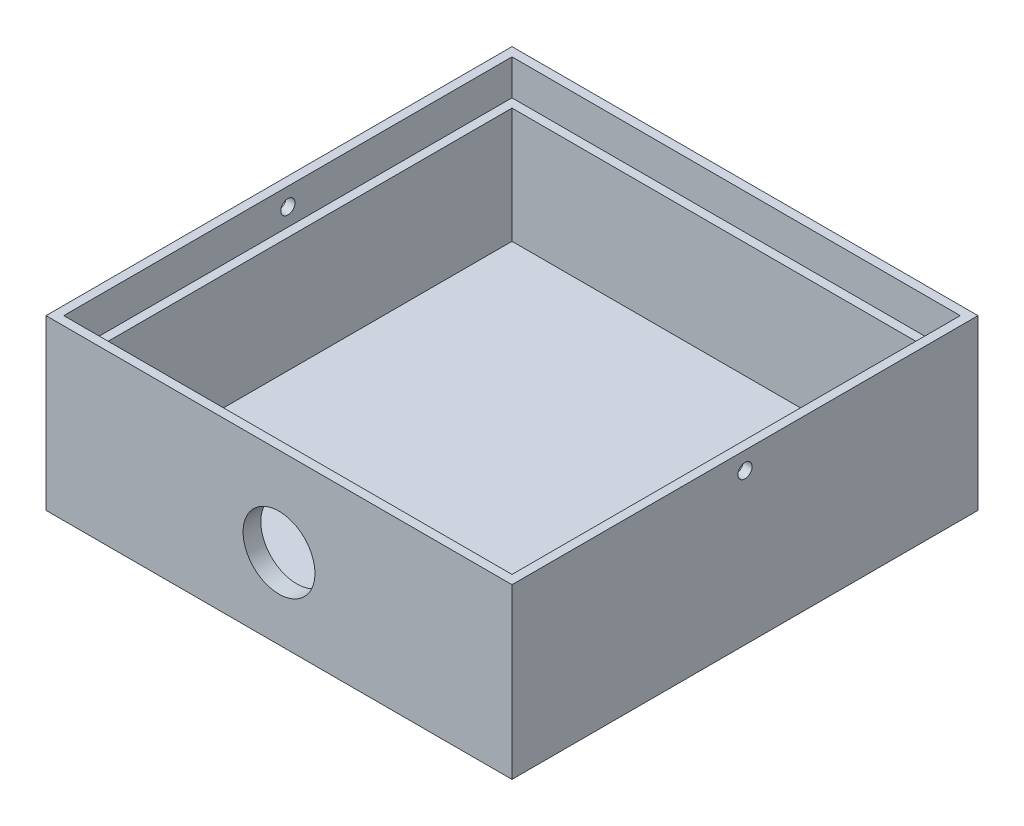
SolidWorks part; units mm, degrees
ref_plane "Front Plane" through (0, 0, 0) normal (0, 0, 1) x (1, 0, 0)
ref_plane "Top Plane" through (0, 0, 0) normal (0, 1, 0) x (1, 0, 0)
ref_plane "Right Plane" through (0, 0, 0) normal (1, 0, 0) x (0, 0, -1)
sketch "Sketch1" plane through (0, 0, 0) normal (0, 1, 0) x (1, 0, 0)
  line L1 (-52.5, 52.5) -> (52.5, 52.5)
  line L2 (-52.5, 52.5) -> (-52.5, -52.5)
  line L3 (-52.5, -52.5) -> (52.5, -52.5)
  line L4 (52.5, 52.5) -> (52.5, -52.5)
  line L5 (-52.5, 52.5) -> (52.5, -52.5) construction
  line L6 (-52.5, -52.5) -> (52.5, 52.5) construction
  point P0 (0, 0)
  dimension "D1" = 105
  dimension "D2" = 105
extrude "Boss-Extrude1" add sketch "Sketch1" along normal blind 38
sketch "Sketch2" plane through (0, 38, 0) normal (0, 1, 0) x (1, 0, 0)
  line L0 (-52.5, 52.5) -> (-52.5, -52.5) construction
  line L1 (-48.5, 48.5) -> (48.5, 48.5)
  line L2 (-48.5, 48.5) -> (-48.5, -48.5)
  line L3 (-48.5, -48.5) -> (48.5, -48.5)
  line L4 (48.5, 48.5) -> (48.5, -48.5)
  line L5 (-48.5, 48.5) -> (48.5, -48.5) construction
  line L6 (-48.5, -48.5) -> (48.5, 48.5) construction
  line L7 (52.5, 52.5) -> (-52.5, 52.5) construction
  point P0 (0, 0)
  dimension "D1" = 4
  dimension "D2" = 4
extrude "Cut-Extrude1" cut sketch "Sketch2" against normal blind 34
sketch "Sketch3" plane through (0, 38, 0) normal (0, 1, 0) x (1, 0, 0)
  line L0 (-52.5, 52.5) -> (-52.5, -52.5) construction
  line L1 (-50.5, 50.5) -> (50.5, 50.5)
  line L2 (-50.5, 50.5) -> (-50.5, -50.5)
  line L3 (-50.5, -50.5) -> (50.5, -50.5)
  line L4 (50.5, 50.5) -> (50.5, -50.5)
  line L5 (-50.5, 50.5) -> (50.5, -50.5) construction
  line L6 (-50.5, -50.5) -> (50.5, 50.5) construction
  line L7 (52.5, 52.5) -> (-52.5, 52.5) construction
  point P0 (0, 0)
  dimension "D1" = 2
  dimension "D2" = 2
extrude "Cut-Extrude2" cut sketch "Sketch3" against normal blind 8
sketch "Sketch5" plane through (52.5, 0, 0) normal (1, 0, 0) x (0, 0, -1)
  line L0 (-52.5, 38) -> (52.5, 38) construction
  circle A0 centre (0, 34) radius 1.6
  dimension "D1" = 3.2
  dimension "D2" = 4
extrude "Cut-Extrude3" cut sketch "Sketch5" against normal through all
sketch "Sketch6" plane through (0, 0, -52.5) normal (0, 0, -1) x (-1, 0, 0)
  line L0 (-52.5, 0) -> (52.5, 0) construction
  line L1 (-12, 0) -> (12, 0)
  line L2 (-12, 0) -> (-12, -5)
  line L4 (12, 0) -> (12, -5)
  line L5 (-52.5, 38) -> (-52.5, 0) construction
  line L8 (-12, -5) -> (-12, -17)
  line L10 (12, -5) -> (12, -17)
  arc A0 (-12, -17) -> (12, -17) centre (0, -17) ccw
  circle A1 centre (0, -17) radius 2.75
  dimension "D5" = 5.5
  dimension "D1" = 5
  dimension "D2" = 24
  dimension "D3" = 40.5
  dimension "D4" = 12
extrude "Boss-Extrude2" add sketch "Sketch6" against normal blind 3
fillet "Fillet1" radius 4 3 edges at (-12, 0, -51) (12, 0, -51) (0, 0, -49.5)
sketch "Sketch7" plane through (0, 0, 48.5) normal (0, 0, -1) x (-1, 0, 0)
  line L0 (-48.5, 30) -> (48.5, 30) construction
  circle A0 centre (0, 18) radius 8.1
  dimension "D1" = 16.2
  dimension "D2" = 12
extrude "Cut-Extrude4" cut sketch "Sketch7" against normal up to next
sketch "Sketch10" plane through (0, 0, 0) normal (0, -1, 0) x (1, 0, 0)
  line L1 (5, -10) -> (0, -10)
  line L2 (5, -10) -> (5, 10)
  line L3 (5, 10) -> (0, 10)
  line L5 (0, -7) -> (2, -7)
  line L7 (0, -3) -> (2, -3)
  line L8 (2, -7) -> (2, -3)
  line L9 (0, 3) -> (2, 3)
  line L11 (0, 7) -> (2, 7)
  line L12 (2, 3) -> (2, 7)
  arc A0 (0, 0) -> (0, -10) centre (0, -5) ccw
  arc A1 (0, 10) -> (0, 0) centre (0, 5) ccw
  arc A2 (0, -3) -> (0, -7) centre (0, -5) ccw
  arc A3 (0, 7) -> (0, 3) centre (0, 5) ccw
  point P5 (0, 0)
  dimension "D3" = 10
  dimension "D4" = 10
  dimension "D5" = 4
  dimension "D6" = 4
  dimension "D1" = 5
  dimension "D2" = 20
  dimension "D7" = 4
  dimension "D8" = 2
  dimension "D9" = 2
  dimension "D10" = 4
extrude "Cut-Extrude5" cut sketch "Sketch10" against normal blind 1
